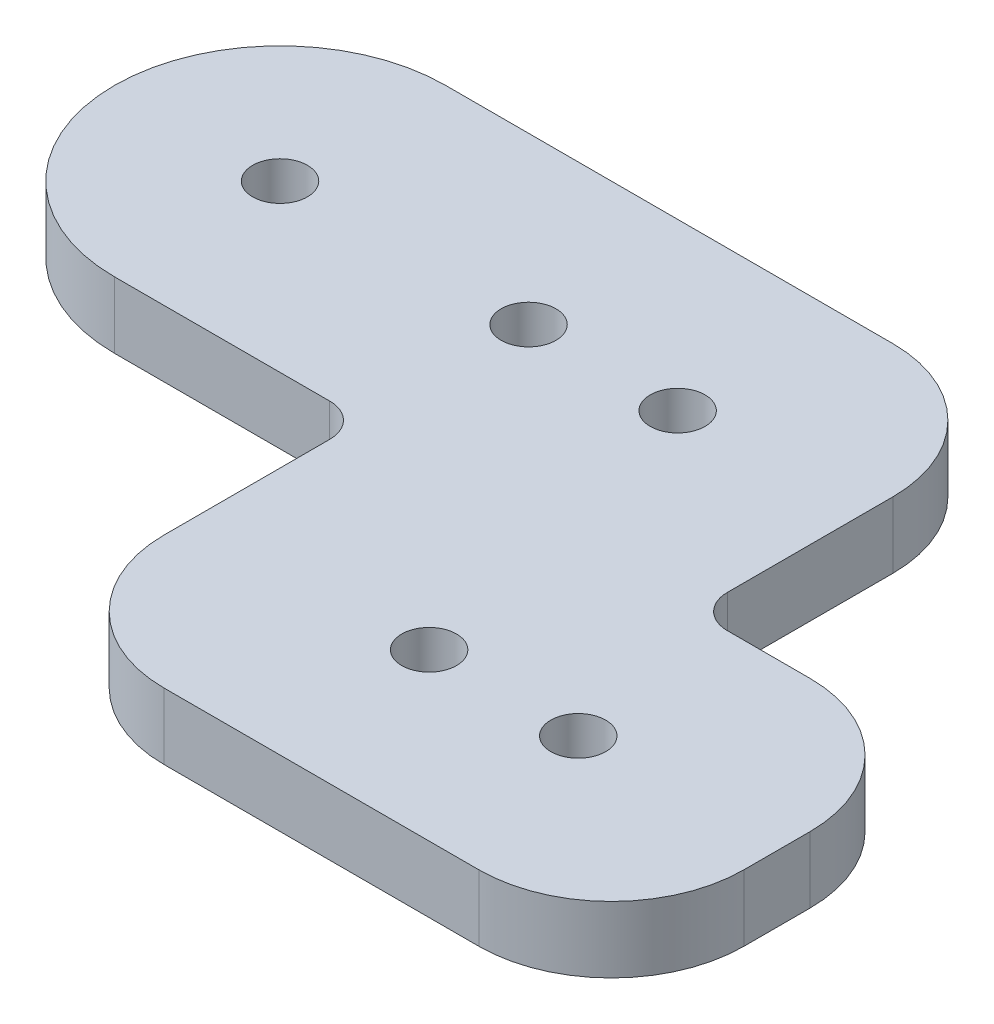
SolidWorks part; units mm, degrees
ref_plane "Front Plane" through (0, 0, 0) normal (0, 0, 1) x (1, 0, 0)
ref_plane "Top Plane" through (0, 0, 0) normal (0, 1, 0) x (1, 0, 0)
ref_plane "Right Plane" through (0, 0, 0) normal (1, 0, 0) x (0, 0, -1)
sketch "Sketch1" plane through (0, 0, 0) normal (0, 1, 0) x (1, 0, 0)
  line L0 (0, 0) -> (30.48, 0) construction
  line L1 (0, -12.7) -> (19.05, -12.7)
  line L2 (0, -12.7) -> (0, 12.7) construction
  line L3 (0, 12.7) -> (44.45, 12.7)
  line L4 (44.45, -12.7) -> (44.45, 12.7)
  line L5 (22.225, 12.7) -> (44.45, 12.7)
  line L7 (19.05, -38.1) -> (35.56, -38.1)
  line L8 (44.45, 12.7) -> (44.45, -12.7)
  line L9 (19.05, -38.1) -> (63.5, -38.1)
  line L10 (19.05, -38.1) -> (19.05, -12.7)
  line L11 (44.45, -12.7) -> (63.5, -12.7)
  line L12 (63.5, -38.1) -> (63.5, -12.7)
  line L13 (63.5, -25.4) -> (25.6515, -25.4) construction
  line L14 (19.05, -12.7) -> (19.05, -38.1)
  arc A0 (0, 12.7) -> (0, -12.7) centre (0, 0) ccw
  circle A1 centre (0, 0) radius 2.1
  circle A2 centre (19.05, 0) radius 2.1
  circle A3 centre (30.48, 0) radius 2.1
  circle A4 centre (36.83, -25.4) radius 2.1
  circle A5 centre (48.26, -25.4) radius 2.1
  point P1 (55.6285, -38.1)
  point P22 (36.3188, -25.1714)
  point P25 (0, 0)
  point P26 (48.26, -25.1616)
  dimension "D6" = 4.2
  dimension "D7" = 4.2
  dimension "D8" = 4.2
  dimension "D11" = 4.2
  dimension "D12" = 4.2
  dimension "D1" = 25.4
  dimension "D2" = 50.8
  dimension "D3" = 44.45
  dimension "D4" = 44.45
  dimension "D5" = 25.4
  dimension "D9" = 19.05
  dimension "D10" = 11.43
  dimension "D13" = 11.43
  dimension "D14" = 6.35
extrude "Boss-Extrude1" add sketch "Sketch1" along normal blind 5.08 contours L3 A0 L1 L10 L7 L9 L12 L11 L4 A5 A4 A3 A2 A1
fillet "Fillet1" radius 2.54 2 edges at (19.05, 2.54, 12.7) (44.45, 2.54, 12.7)
fillet "Fillet2" radius 10.16 4 edges at (19.05, 2.54, 38.1) (44.45, 2.54, -12.7) (63.5, 2.54, 12.7) (63.5, 2.54, 38.1)
